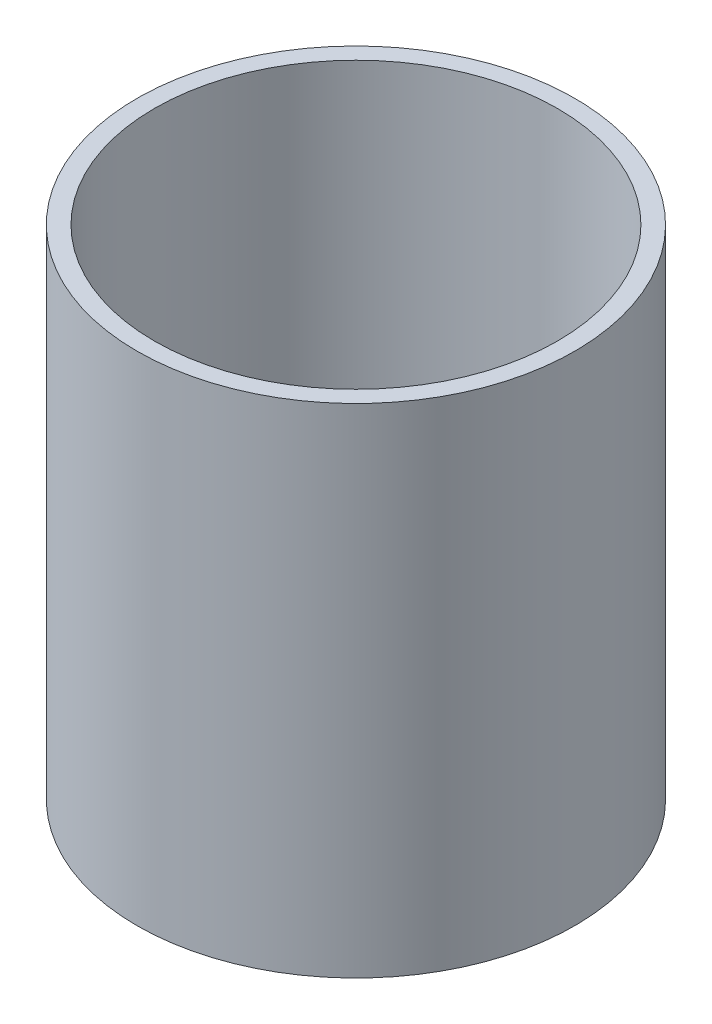
SolidWorks part; units mm, degrees
material "Chrome Stainless Steel"
ref_plane "Front Plane" through (0, 0, 0) normal (0, 0, 1) x (1, 0, 0)
ref_plane "Top Plane" through (0, 0, 0) normal (0, 1, 0) x (1, 0, 0)
ref_plane "Right Plane" through (0, 0, 0) normal (1, 0, 0) x (0, 0, -1)
sketch "Sketch1" plane through (0, 0, 0) normal (0, 1, 0) x (1, 0, 0)
  circle A0 centre (0, 0) radius 20.25
  circle A1 centre (0, 0) radius 22
  dimension "D1" = 44
  dimension "D2" = 40.5
extrude "Boss-Extrude1" add sketch "Sketch1" along normal blind 50
